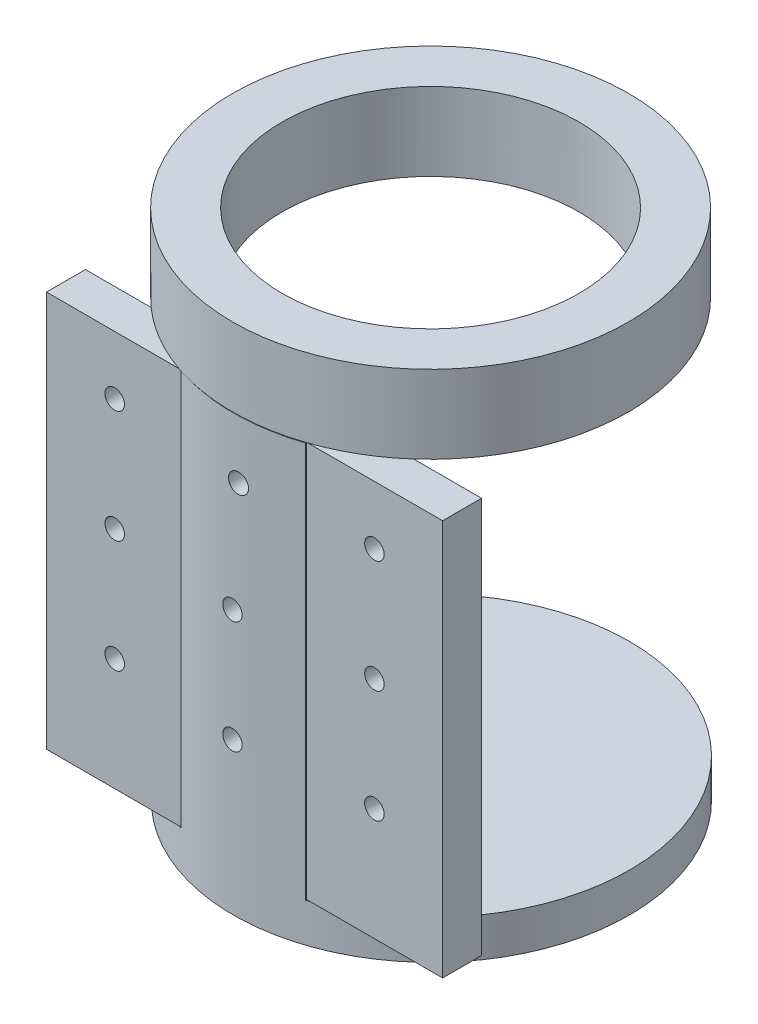
SolidWorks part; units mm, degrees
ref_plane "Front Plane" through (0, 0, 0) normal (0, 0, 1) x (1, 0, 0)
ref_plane "Top Plane" through (0, 0, 0) normal (0, 1, 0) x (1, 0, 0)
ref_plane "Right Plane" through (0, 0, 0) normal (1, 0, 0) x (0, 0, -1)
sketch "Sketch1" plane through (0, 0, 0) normal (0, 1, 0) x (1, 0, 0)
  circle A0 centre (0, 0) radius 50.8
  circle A1 centre (0, 0) radius 38.1
  dimension "D1" = 101.6
  dimension "D2" = 76.2
extrude "Boss-Extrude1" add sketch "Sketch1" along normal blind 20
sketch "Sketch2" plane through (0, 0, 0) normal (0, -1, 0) x (1, 0, 0)
  line L1 (-15.6617, 48.3255) -> (16.2462, 48.3255)
  line L2 (-15.6617, 48.3255) -> (-15.6617, 38.0246)
  line L3 (-15.6617, 38.0246) -> (16.2462, 38.0246)
  line L4 (16.2462, 48.3255) -> (16.2462, 38.0246)
  circle A0 centre (0, 0) radius 50.8 construction
extrude "Boss-Extrude2" add sketch "Sketch2" along normal blind 101.6
sketch "Sketch3" plane through (0, -101.6, 0) normal (0, -1, 0) x (1, 0, 0)
  circle A0 centre (0.2923, 0.0779) radius 50.8169
  line M5 (16.2462, 48.3255) -> (-15.6617, 48.3255)
extrude "Boss-Extrude3" add sketch "Sketch3" against normal blind 101.6 contours A0 M5
sketch "Sketch4" plane through (0, -101.6, 0) normal (0, -1, 0) x (1, 0, 0)
  circle A0 centre (0.2923, 0.0779) radius 50.8169
extrude "Boss-Extrude4" add sketch "Sketch4" along normal blind 10
ref_plane "Plane1" through (0, 0, 50.0246) normal (0, 0, -1) x (-1, 0, 0)
sketch "Sketch6" plane through (0, 0, 38.0246) normal (0, 0, -1) x (-1, 0, 0)
  line L1 (15.6617, 0) -> (50.5246, 0)
  line L2 (15.6617, 0) -> (15.6617, -101.6)
  line L3 (15.6617, -101.6) -> (50.5246, -101.6)
  line L4 (50.5246, 0) -> (50.5246, -101.6)
extrude "Boss-Extrude5" add sketch "Sketch6" against normal blind 10
sketch "Sketch7" plane through (0, 0, 38.0246) normal (0, 0, -1) x (-1, 0, 0)
  line L1 (-16.2462, 0) -> (-51.1092, 0)
  line L2 (-16.2462, 0) -> (-16.2462, -101.6)
  line L3 (-16.2462, -101.6) -> (-51.1092, -101.6)
  line L4 (-51.1092, 0) -> (-51.1092, -101.6)
extrude "Boss-Extrude6" add sketch "Sketch7" against normal blind 10
sketch "Sketch8" plane through (0, 0, 48.0246) normal (0, 0, 1) x (1, 0, 0)
  line L2 (51.1092, -101.6) -> (17.1288, -101.6) construction
  line L3 (51.1092, 0) -> (51.1092, -101.6) construction
  circle A0 centre (33.6092, -15) radius 2.5
  circle A1 centre (33.6092, -43.8667) radius 2.5
  circle A2 centre (33.6092, -72.7333) radius 2.5
  dimension "D1" = 5
  dimension "D2" = 5
  dimension "D3" = 5
  dimension "D4" = 28.8667
  dimension "D5" = 57.7333
  dimension "D6" = 86.6
  dimension "D7" = 17.5
  dimension "D8" = 17.5
  dimension "D9" = 17.5
extrude "Cut-Extrude1" cut sketch "Sketch8" against normal through all both and the other way through all
sketch "Sketch10" plane through (0, 0, 38.0246) normal (0, 0, -1) x (-1, 0, 0)
  circle A0 centre (-33.6092, -15) radius 5
  circle A1 centre (-33.6092, -43.8667) radius 5
  circle A2 centre (-33.6092, -72.7333) radius 5
  dimension "D1" = 10
  dimension "D2" = 10
  dimension "D3" = 10
extrude "Cut-Extrude2" cut sketch "Sketch10" against normal blind 5.15
sketch "Sketch11" plane through (0, 0, 48.0246) normal (0, 0, 1) x (1, 0, 0)
  line L0 (-50.5246, -101.6) -> (-50.5246, 0) construction
  line L1 (51.1092, -101.6) -> (-50.5246, -101.6) construction
  line L4 (-16.5443, -101.6) -> (-50.5246, -101.6) construction
  circle A0 centre (-33.0246, -15) radius 2.5
  circle A1 centre (-33.0246, -43.8667) radius 2.5
  circle A2 centre (-33.0246, -72.7333) radius 2.5
  dimension "D1" = 5
  dimension "D2" = 5
  dimension "D3" = 5
  dimension "D4" = 17.5
  dimension "D5" = 17.5
  dimension "D6" = 17.5
  dimension "D7" = 86.6
  dimension "D8" = 57.7333
  dimension "D9" = 28.8667
extrude "Cut-Extrude3" cut sketch "Sketch11" against normal through all both and the other way through all
sketch "Sketch12" plane through (0, 0, 38.0246) normal (0, 0, -1) x (-1, 0, 0)
  circle A0 centre (33.0246, -15) radius 5
  circle A1 centre (33.0246, -43.8667) radius 5
  circle A2 centre (33.0246, -72.7333) radius 5
  dimension "D1" = 10
  dimension "D2" = 10
  dimension "D3" = 10
extrude "Cut-Extrude4" cut sketch "Sketch12" against normal blind 5.15
sketch "Sketch13" plane through (0, 0, 38.0246) normal (0, 0, -1) x (-1, 0, 0)
  line L0 (33.5072, -101.6) -> (-34.0917, -101.6) construction
  circle A0 centre (-1.5496, -15) radius 2.5
  circle A1 centre (0, -43.8667) radius 2.5
  circle A2 centre (0, -72.7333) radius 2.5
  dimension "D1" = 5
  dimension "D2" = 5
  dimension "D3" = 5
  dimension "D4" = 28.8667
  dimension "D5" = 57.7333
  dimension "D6" = 86.6
extrude "Cut-Extrude5" cut sketch "Sketch13" against normal through all both and the other way through all
sketch "Sketch14" plane through (0, 0, 38.0246) normal (0, 0, -1) x (-1, 0, 0)
  circle A0 centre (-1.5496, -15) radius 5
  circle A1 centre (0, -43.8667) radius 5
  circle A2 centre (0, -72.7333) radius 5
  dimension "D1" = 10
  dimension "D2" = 10
  dimension "D3" = 10
extrude "Cut-Extrude6" cut sketch "Sketch14" against normal blind 5.15
